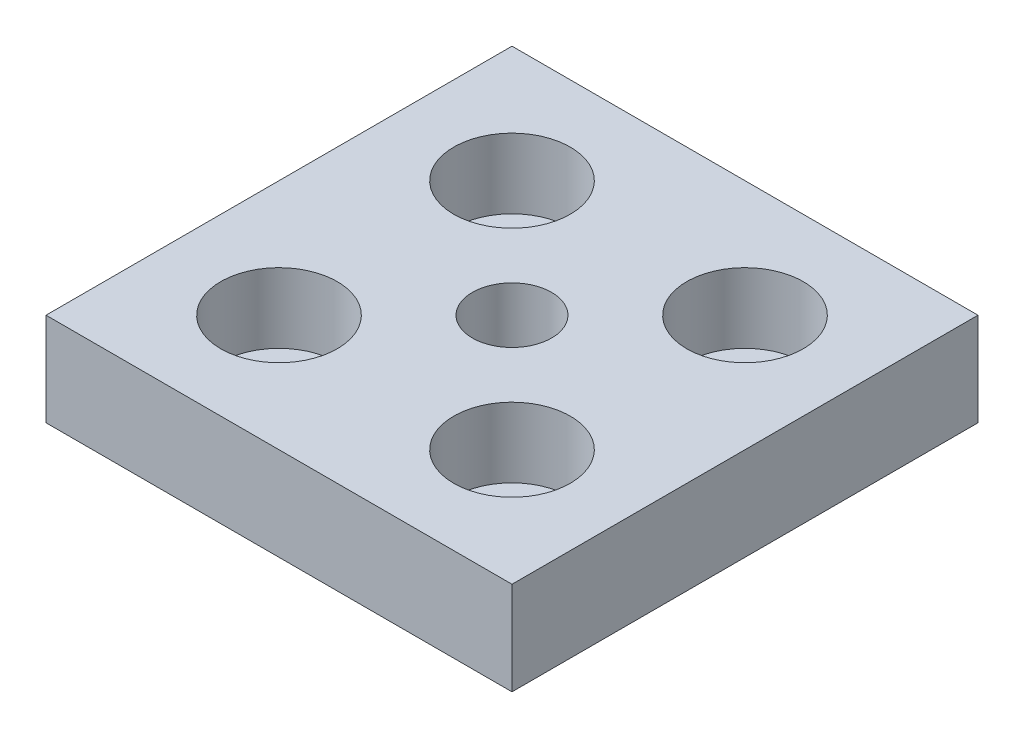
SolidWorks part; units mm, degrees
material "Алюминиевый сплав"
ref_plane "Спереди" through (0, 0, 0) normal (0, 0, 1) x (1, 0, 0)
ref_plane "Сверху" through (0, 0, 0) normal (0, 1, 0) x (1, 0, 0)
ref_plane "Справа" through (0, 0, 0) normal (1, 0, 0) x (0, 0, -1)
sketch "Эскиз1" plane through (0, 0, 0) normal (0, 1, 0) x (1, 0, 0)
  line L1 (-30, -30) -> (30, -30)
  line L2 (-30, -30) -> (-30, 30)
  line L3 (-30, 30) -> (30, 30)
  line L4 (30, -30) -> (30, 30)
  line L5 (-30, -30) -> (30, 30) construction
  line L6 (-30, 30) -> (30, -30) construction
  point P0 (0, 0)
  dimension "D1" = 60
extrude "Бобышка-Вытянуть1" add sketch "Эскиз1" along normal blind 12
hole_wizard "Отверстие обработанное метчиком M121" positions "Эскиз8" profile "Эскиз9" tap size "M12" standard "ISO" end condition up to next
sketch "Эскиз8" plane through (0, 12, 0) normal (0, 1, 0) x (1, 0, 0)
  point P0 (0, 0)
sketch "Эскиз9" plane through (0, 12, 0) normal (1, 0, 0) x (0, 0, 1)
  line L0 (0, 0) -> (0, 12)
  line L1 (0, 12) -> (5.1, 12)
  line L2 (5.1, 12) -> (5.1, 0)
  line L5 (5.1, 0) -> (0, 0)
  line L11 (0, -6.35) -> (0, 107.95) construction
  dimension "Диаметр проходного сверла" = 10.2
  dimension "Глубина проходного сверла" = 12
cosmetic thread "Отверстие резьбы3" parameters "D2"=12
sketch "Эскиз12" plane through (0, 12, 0) normal (0, 1, 0) x (1, 0, 0)
  line L1 (15, -15) -> (-15, -15) construction
  line L2 (15, -15) -> (15, 15) construction
  line L3 (15, 15) -> (-15, 15) construction
  line L4 (-15, -15) -> (-15, 15) construction
  line L5 (15, -15) -> (-15, 15) construction
  line L6 (15, 15) -> (-15, -15) construction
  circle A0 centre (-15, 15) radius 4.5
  circle A1 centre (15, 15) radius 4.5
  circle A2 centre (15, -15) radius 4.5
  circle A3 centre (-15, -15) radius 4.5
  point P0 (0, 0)
  dimension "D2" = 9
  dimension "D1" = 30
extrude "Вырез-Вытянуть1" cut sketch "Эскиз12" against normal through all
sketch "Эскиз13" plane through (0, 12, 0) normal (0, 1, 0) x (1, 0, 0)
  circle A0 centre (-15, 15) radius 7.5
  circle A1 centre (15, 15) radius 7.5
  circle A2 centre (15, -15) radius 7.5
  circle A3 centre (-15, -15) radius 7.5
  dimension "D1" = 15
extrude "Вырез-Вытянуть2" cut sketch "Эскиз13" against normal blind 9
